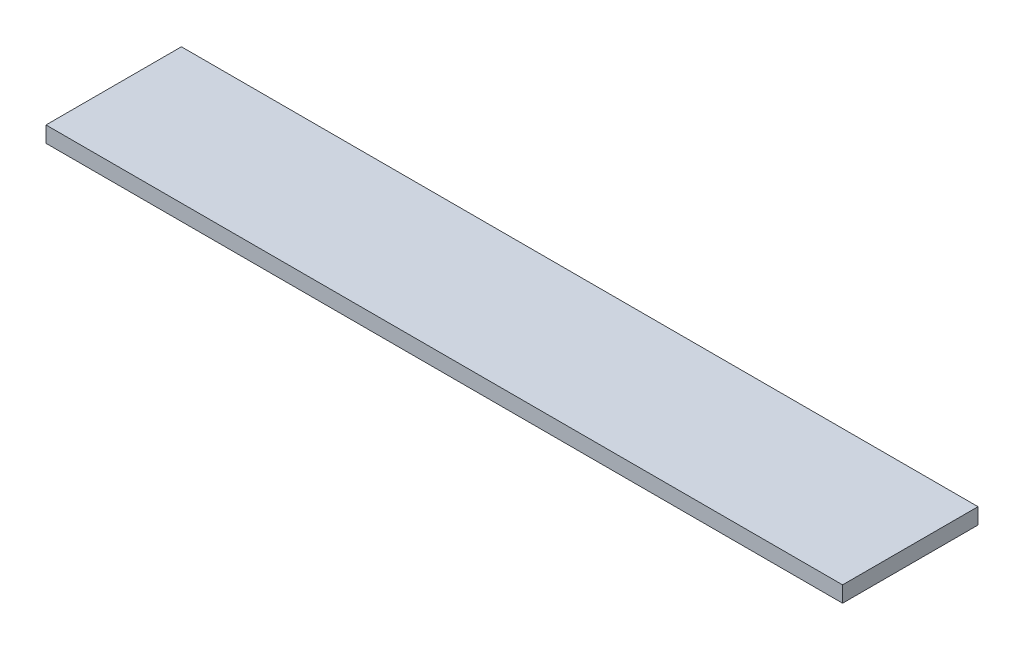
SolidWorks part; units mm, degrees
ref_plane "Front Plane" through (0, 0, 0) normal (0, 0, 1) x (1, 0, 0)
ref_plane "Top Plane" through (0, 0, 0) normal (0, 1, 0) x (1, 0, 0)
ref_plane "Right Plane" through (0, 0, 0) normal (1, 0, 0) x (0, 0, -1)
sketch "Sketch1" plane through (0, 0, 0) normal (0, 1, 0) x (1, 0, 0)
  line L1 (-250, 42.5) -> (250, 42.5)
  line L2 (-250, 42.5) -> (-250, -42.5)
  line L3 (-250, -42.5) -> (250, -42.5)
  line L4 (250, 42.5) -> (250, -42.5)
  line L5 (-250, 42.5) -> (250, -42.5) construction
  line L6 (-250, -42.5) -> (250, 42.5) construction
  point P0 (0, 0)
  dimension "D1" = 85
  dimension "D2" = 500
extrude "Boss-Extrude1" add sketch "Sketch1" against normal blind 10
